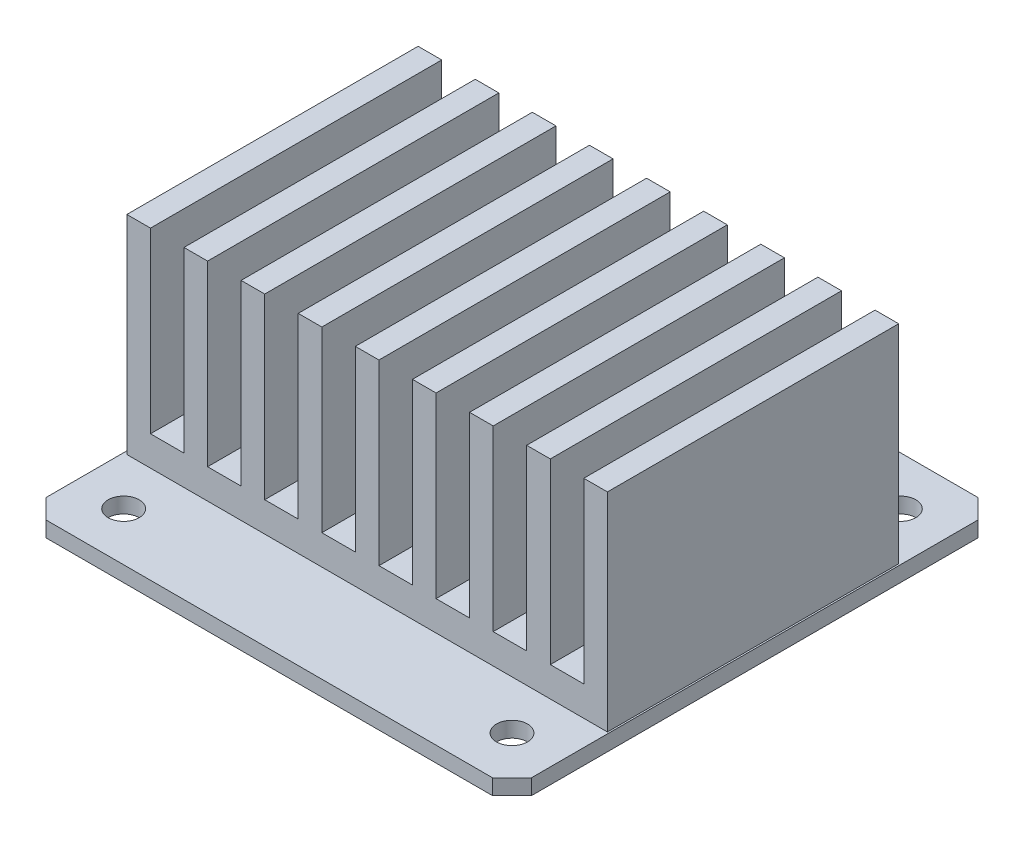
SolidWorks part; units mm, degrees
ref_plane "Ön Düzlem" through (0, 0, 0) normal (0, 0, 1) x (1, 0, 0)
ref_plane "Üst Düzlem" through (0, 0, 0) normal (0, 1, 0) x (1, 0, 0)
ref_plane "Sağ Düzlem" through (0, 0, 0) normal (1, 0, 0) x (0, 0, -1)
sketch "Sketch1" plane through (0, 0, 0) normal (0, 1, 0) x (1, 0, 0)
  line L0 (-25, 23) -> (-23, 25)
  line L1 (-23, 25) -> (23, 25)
  line L2 (-25, 23) -> (-25, -23)
  line L3 (-23, -25) -> (23, -25)
  line L4 (25, 23) -> (25, -23)
  line L5 (-25, 25) -> (25, -25) construction
  line L6 (-25, -25) -> (25, 25) construction
  line L7 (23, 25) -> (25, 23)
  line L8 (23, -25) -> (25, -23)
  line L9 (-25, -23) -> (-23, -25)
  line L11 (-20, 20) -> (20, 20) construction
  line L12 (-20, 20) -> (-20, -20) construction
  line L13 (-20, -20) -> (20, -20) construction
  line L14 (20, 20) -> (20, -20) construction
  line L15 (-20, 20) -> (20, -20) construction
  line L16 (-20, -20) -> (20, 20) construction
  circle A0 centre (20, 20) radius 1.6
  circle A1 centre (-20, 20) radius 1.6
  circle A2 centre (-20, -20) radius 1.6
  circle A3 centre (20, -20) radius 1.6
  point P0 (0, 0)
  point P14 (0, 0)
  dimension "D4" = 3.2
  dimension "D1" = 50
  dimension "D2" = 50
  dimension "D3" = 40
extrude "Boss-Extrude1" add sketch "Sketch1" along normal blind 1.6
sketch "Sketch2" plane through (0, 0, 0) normal (0, 0, 1) x (1, 0, 0)
  line L0 (-24.6715, 1.6) -> (-24.6715, 23.0156)
  line L2 (24.8285, 23.0156) -> (24.8285, 1.6)
  line L3 (24.8285, 1.6) -> (-24.6715, 1.6)
  line L4 (-24.6715, 23.0156) -> (-22.238, 23.0156)
  line L5 (-22.238, 23.0156) -> (-22.238, 4.6668)
  line L6 (-22.238, 4.6668) -> (-18.7882, 4.6668)
  line L7 (-18.7882, 4.6668) -> (-18.7882, 23.0156)
  line L8 (-18.7882, 23.0156) -> (-16.3547, 23.0156)
  line L9 (-16.3547, 23.0156) -> (-16.3547, 4.6668)
  line L10 (-16.3547, 4.6668) -> (-12.9049, 4.6668)
  line L11 (-12.9049, 4.6668) -> (-12.9049, 23.0156)
  line L12 (-12.9049, 23.0156) -> (-10.4714, 23.0156)
  line L13 (-10.4714, 23.0156) -> (-10.4714, 4.6668)
  line L14 (-10.4714, 4.6668) -> (-7.0216, 4.6668)
  line L15 (-7.0216, 4.6668) -> (-7.0216, 23.0156)
  line L16 (-7.0216, 23.0156) -> (-4.5881, 23.0156)
  line L17 (-4.5881, 23.0156) -> (-4.5881, 4.6668)
  line L18 (-4.5881, 4.6668) -> (-1.1383, 4.6668)
  line L19 (-1.1383, 4.6668) -> (-1.1383, 23.0156)
  line L20 (-1.1383, 23.0156) -> (1.2952, 23.0156)
  line L21 (1.2952, 23.0156) -> (1.2952, 4.6668)
  line L22 (1.2952, 4.6668) -> (4.745, 4.6668)
  line L23 (4.745, 4.6668) -> (4.745, 23.0156)
  line L24 (4.745, 23.0156) -> (7.1785, 23.0156)
  line L25 (7.1785, 23.0156) -> (7.1785, 4.6668)
  line L26 (7.1785, 4.6668) -> (10.6283, 4.6668)
  line L27 (10.6283, 4.6668) -> (10.6283, 23.0156)
  line L28 (10.6283, 23.0156) -> (13.0618, 23.0156)
  line L29 (13.0618, 23.0156) -> (13.0618, 4.6668)
  line L30 (13.0618, 4.6668) -> (16.5116, 4.6668)
  line L31 (16.5116, 4.6668) -> (16.5116, 23.0156)
  line L32 (16.5116, 23.0156) -> (18.9451, 23.0156)
  line L33 (18.9451, 23.0156) -> (18.9451, 4.6668)
  line L34 (18.9451, 4.6668) -> (22.3949, 4.6668)
  line L35 (22.3949, 4.6668) -> (22.3949, 23.0156)
  line L36 (22.3949, 23.0156) -> (24.8285, 23.0156)
  line L37 (-25, 1.6) -> (-23, 1.6) construction
  point P3 (-20.79, 24.7447)
  point P39 (25.9099, 24.2792)
  point P40 (20.9451, 25.0033)
  point P41 (21.9278, 24.8998)
  point P42 (25, 24.7964)
  point P43 (23.5827, 24.7964)
  point P44 (-22.7035, 24.693)
  point P45 (-19.4971, 24.4344)
  point P46 (-16.0838, 24.3827)
  point P47 (-12.6188, 24.5378)
  point P48 (-9.5675, 24.331)
  point P49 (-5.844, 24.1758)
  point P50 (-2.4307, 24.1241)
  point P51 (1.2412, 24.0724)
  point P52 (2.9996, 23.8655)
  point P53 (6.568, 23.7104)
  point P54 (9.5158, 23.9172)
  point P55 (12.8774, 23.7104)
  point P56 (14.6357, 23.7104)
  point P57 (17.0147, 23.5035)
  point P58 (19.3419, 23.2449)
  point P59 (21.3589, 23.0898)
  point P60 (12.2568, 23.038)
  point P61 (-24.7996, 1.6)
  point P64 (-24.6715, 1.6)
  dimension "D1" = 49.5
extrude "Boss-Extrude2" add sketch "Sketch2" along normal blind 15 and the other way blind 15
sketch "Sketch3" plane through (0, 0, 0) normal (0, -1, 0) x (1, 0, 0)
  circle A0 centre (-12.3815, -18.4719) radius 4.4841
extrude "Boss-Extrude3" add sketch "Sketch3" along normal blind 15
sketch "Sketch4" plane through (0, 0, 0) normal (0, -1, 0) x (1, 0, 0)
  line L1 (-3.4802, -15.4602) -> (14.3224, -15.4602)
  line L2 (-3.4802, -15.4602) -> (-3.4802, -22.2867)
  line L3 (-3.4802, -22.2867) -> (14.3224, -22.2867)
  line L4 (14.3224, -15.4602) -> (14.3224, -22.2867)
  line L5 (-3.4802, -15.4602) -> (14.3224, -22.2867) construction
  line L6 (-3.4802, -22.2867) -> (14.3224, -15.4602) construction
  point P0 (5.4211, -18.8734)
extrude "Boss-Extrude4" add sketch "Sketch4" along normal blind 10
